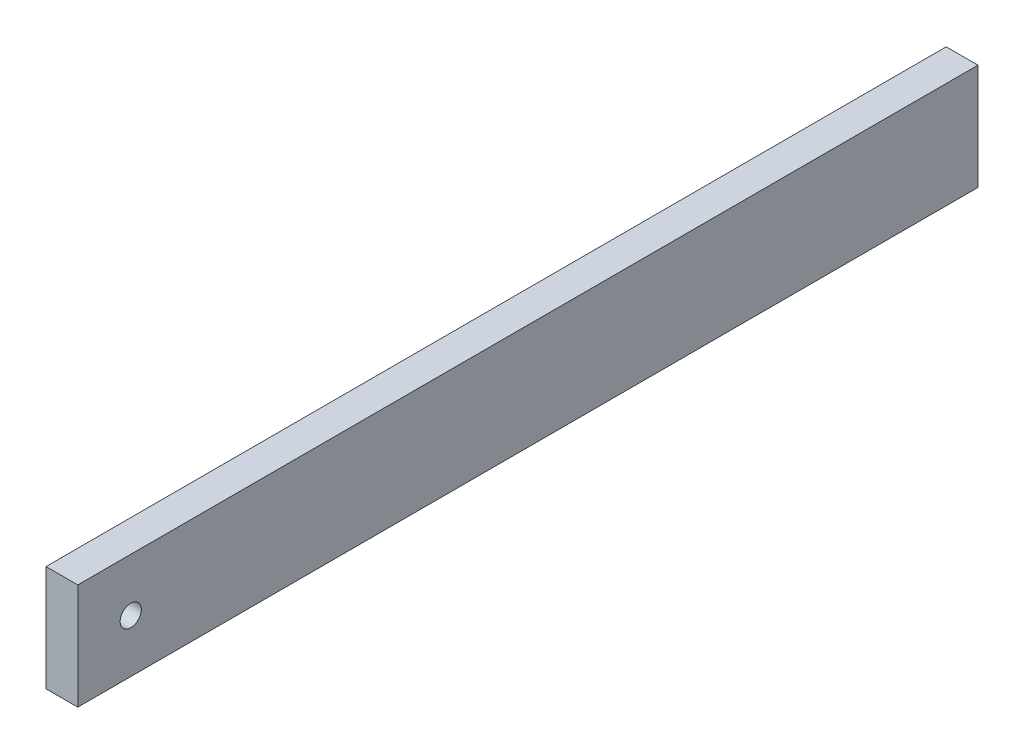
SolidWorks part; units mm, degrees
ref_plane "Plan de face" through (0, 0, 0) normal (0, 0, 1) x (1, 0, 0)
ref_plane "Plan de dessus" through (0, 0, 0) normal (0, 1, 0) x (1, 0, 0)
ref_plane "Plan de droite" through (0, 0, 0) normal (1, 0, 0) x (0, 0, -1)
sketch "Esquisse1" plane through (0, 0, 0) normal (1, 0, 0) x (0, 0, -1)
  line L0 (5, 10) -> (5, 0) construction
  line L1 (0, 0) -> (85, 0)
  line L2 (0, 0) -> (0, 10)
  line L3 (0, 10) -> (85, 10)
  line L4 (85, 0) -> (85, 10)
  circle A0 centre (5, 5) radius 1
  point P9 (0, 0)
  point P10 (5, 5)
  dimension "D3" = 2
  dimension "D1" = 80
  dimension "D2" = 10
  dimension "D4" = 5
extrude "Boss.-Extru.1" add sketch "Esquisse1" along normal blind 3
